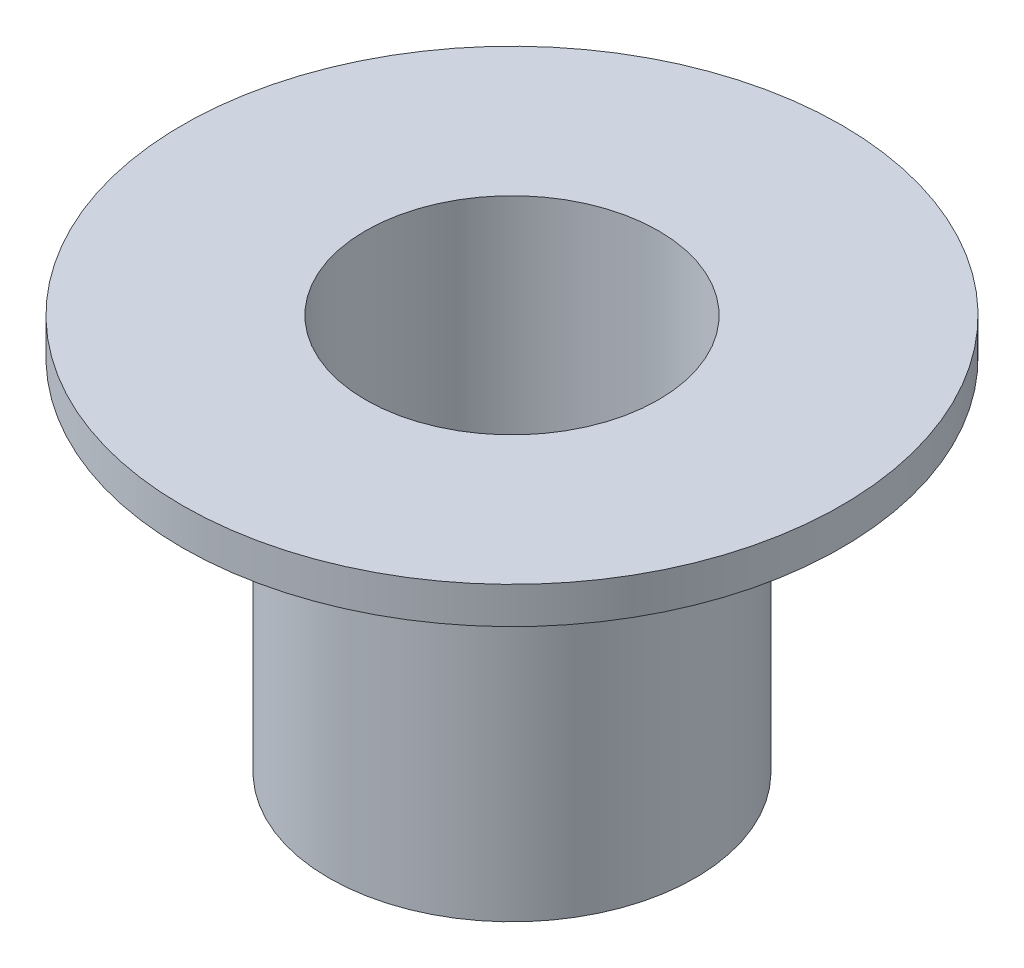
SolidWorks part; units mm, degrees
ref_plane "Front" through (0, 0, 0) normal (0, 0, 1) x (1, 0, 0)
ref_plane "Top" through (0, 0, 0) normal (0, 1, 0) x (1, 0, 0)
ref_plane "Right" through (0, 0, 0) normal (1, 0, 0) x (0, 0, -1)
sketch "Sketch1" plane through (0, 0, 0) normal (0, 1, 0) x (1, 0, 0)
  circle A0 centre (0, 0) radius 5
  dimension "D1" = 10
extrude "Boss-Extrude1" add sketch "Sketch1" against normal blind 9.81
sketch "Sketch2" plane through (0, 0, 0) normal (0, 1, 0) x (1, 0, 0)
  circle A0 centre (0, 0) radius 9
  dimension "D1" = 18
extrude "Boss-Extrude2" add sketch "Sketch2" along normal blind 1
sketch "Sketch3" plane through (0, 1, 0) normal (0, 1, 0) x (1, 0, 0)
  circle A0 centre (0, 0) radius 4
  dimension "D1" = 8
extrude "Cut-Extrude1" cut sketch "Sketch3" against normal blind 15.72 contours A0
